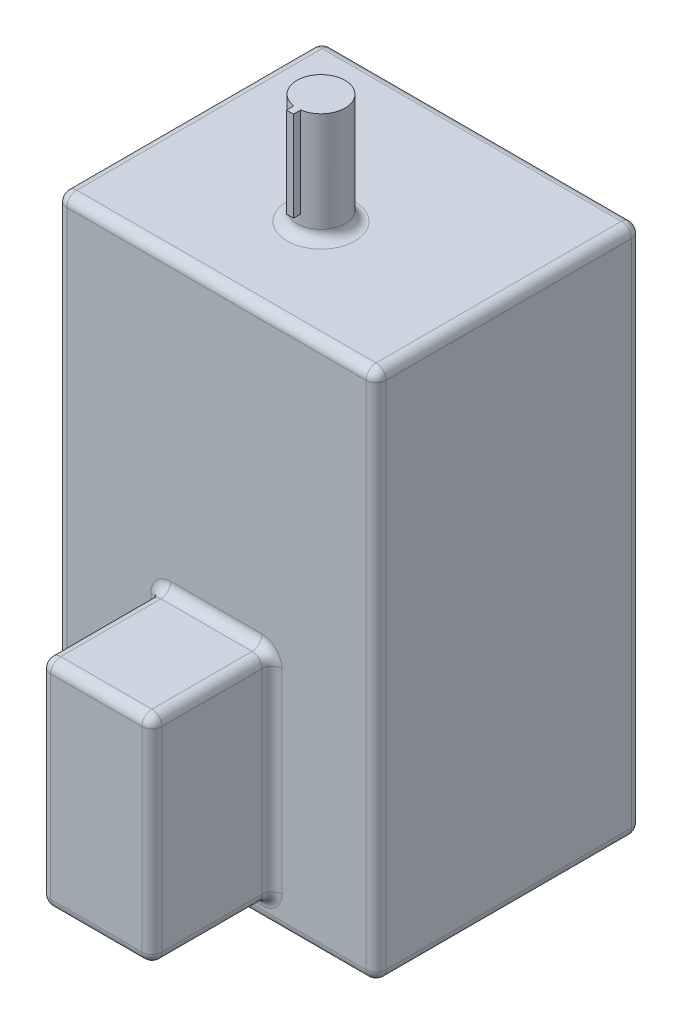
SolidWorks part; units mm, degrees
ref_plane "Front Plane" through (0, 0, 0) normal (0, 0, 1) x (1, 0, 0)
ref_plane "Top Plane" through (0, 0, 0) normal (0, 1, 0) x (1, 0, 0)
ref_plane "Right Plane" through (0, 0, 0) normal (1, 0, 0) x (0, 0, -1)
sketch "Sketch1" plane through (0, 0, 0) normal (0, 0, 1) x (1, 0, 0)
  line L1 (-159.5, -265) -> (159.5, -265)
  line L2 (-159.5, -265) -> (-159.5, 265)
  line L3 (-159.5, 265) -> (159.5, 265)
  line L4 (159.5, -265) -> (159.5, 265)
  line L5 (-159.5, -265) -> (159.5, 265) construction
  line L6 (-159.5, 265) -> (159.5, -265) construction
  point P0 (0, 0)
  dimension "D1" = 319
  dimension "D2" = 530
extrude "Boss-Extrude1" add sketch "Sketch1" along normal blind 265
sketch "Sketch2" plane through (0, 0, 265) normal (0, 0, 1) x (1, 0, 0)
  line L1 (-55.5485, -26.5924) -> (55.5485, -26.5924)
  line L2 (-55.5485, -26.5924) -> (-55.5485, -241.6952)
  line L3 (-55.5485, -241.6952) -> (55.5485, -241.6952)
  line L4 (55.5485, -26.5924) -> (55.5485, -241.6952)
  line L5 (-55.5485, -26.5924) -> (55.5485, -241.6952) construction
  line L6 (-55.5485, -241.6952) -> (55.5485, -26.5924) construction
  point P0 (0, -134.1438)
extrude "Boss-Extrude2" add sketch "Sketch2" along normal blind 120
sketch "Sketch3" plane through (0, 265, 0) normal (0, 1, 0) x (1, 0, 0)
  line L0 (159.5, 0) -> (-159.5, 0) construction
  line L1 (159.5, -265) -> (159.5, 0) construction
  circle A0 centre (-0.5, -160) radius 24
  dimension "D1" = 48
  dimension "D2" = 160
  dimension "D3" = 160
extrude "Boss-Extrude3" add sketch "Sketch3" along normal blind 110
sketch "Sketch4" plane through (0, 375, 0) normal (0, 1, 0) x (1, 0, 0)
  line L1 (-4, -177) -> (3, -177)
  line L2 (-4, -177) -> (-4, -191)
  line L3 (-4, -191) -> (3, -191)
  line L4 (3, -177) -> (3, -191)
  line L5 (-4, -177) -> (3, -191) construction
  line L6 (-4, -191) -> (3, -177) construction
  circle A0 centre (-0.5, -160) radius 24 construction
  circle A1 centre (-0.5, -160) radius 24 construction
  point P0 (-0.5, -184)
  dimension "D1" = 14
  dimension "D2" = 7
extrude "Boss-Extrude4" add sketch "Sketch4" against normal blind 90
fillet "Fillet1" radius 10 25 edges at (-159.5, 0, 0) (-55.5485, -26.5924, 325) (-55.5485, -134.1438, 385) (0, -26.5924, 385) (55.5485, -134.1438, 385) (55.5485, -26.5924, 325) (-55.5485, -241.6952, 325) (0, -241.6952, 385) (55.5485, -241.6952, 325) (-159.5, -265, 132.5) (0, -265, 0) (-159.5, 265, 132.5) (0, 265, 0) (-0.5, 265, 136) (0, -26.5924, 265) (-55.5485, -134.1438, 265) (0, -241.6952, 265) (0, -265, 265) (-159.5, 0, 265) (0, 265, 265) (159.5, -265, 132.5) (159.5, 0, 265) (159.5, 265, 132.5) (159.5, 0, 0) (55.5485, -134.1438, 265)
